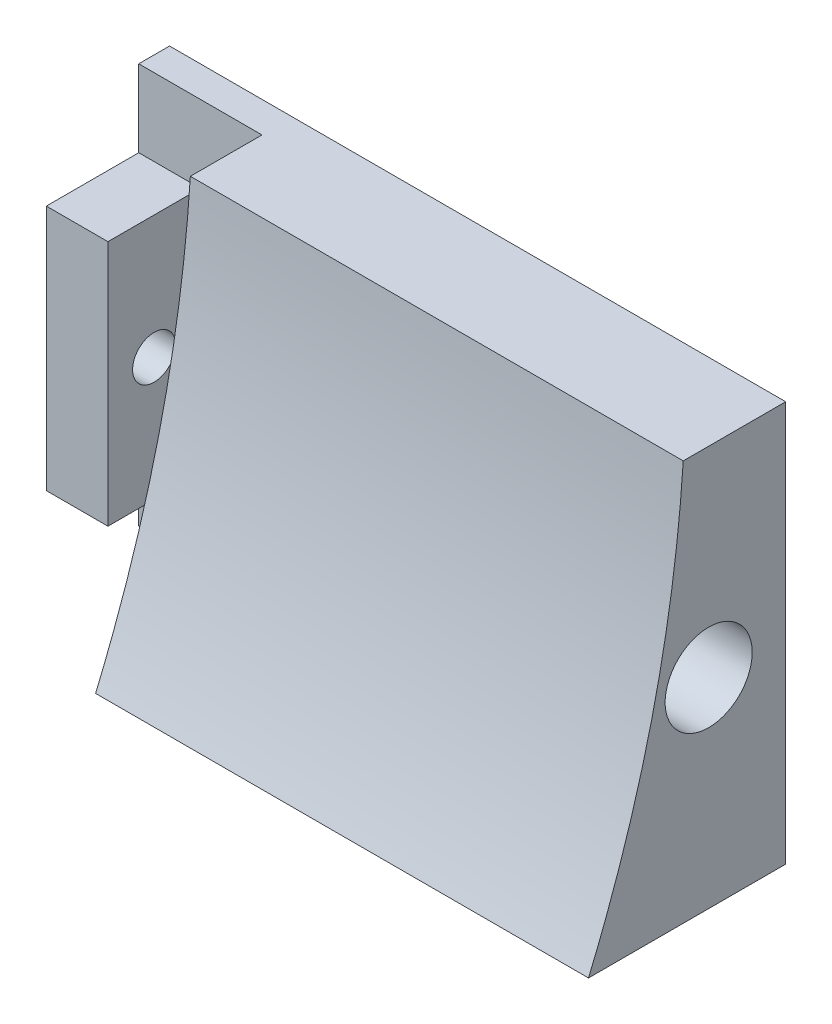
SolidWorks part; units mm, degrees
ref_plane "Plan de face" through (0, 0, 0) normal (0, 0, 1) x (1, 0, 0)
ref_plane "Plan de dessus" through (0, 0, 0) normal (0, 1, 0) x (1, 0, 0)
ref_plane "Plan de droite" through (0, 0, 0) normal (1, 0, 0) x (0, 0, -1)
sketch "Esquisse1" plane through (0, 0, 0) normal (0, 0, 1) x (1, 0, 0)
  line L0 (28, -11.85) -> (28, -37.85)
  line L1 (0, 0) -> (0, -49.7) construction
  line L2 (28, -24.85) -> (-3.4703, -24.85) construction
  line L3 (0, -24.85) -> (-8.0205, -24.85) construction
  line L4 (-12, -11.85) -> (-12, -37.85) construction
  line L5 (28, -11.85) -> (-12, -11.85)
  line L6 (-12, -11.85) -> (-12, -37.85)
  line L7 (-12, -37.85) -> (28, -37.85)
  dimension "D1" = 49.7
  dimension "D2" = 28
  dimension "D3" = 26
  dimension "D4" = 0
  dimension "D5" = 12
extrude "Boss.-Extru.1" add sketch "Esquisse1" along normal blind 2
sketch "Esquisse2" plane through (-12, 0, 0) normal (-1, 0, 0) x (0, 0, 1)
  line L0 (2, -24.85) -> (0, -24.85) construction
  line L1 (2, -11.85) -> (2, -37.85) construction
  line L2 (0, -11.85) -> (0, -37.85) construction
  line L3 (0, -32.85) -> (8, -32.85) construction
  line L4 (8, -32.85) -> (8, -24.85) construction
  line L5 (8, -24.85) -> (2, -24.85) construction
  line L6 (4, -32.85) -> (4, -24.85) construction
  line L7 (2, -32.85) -> (2, -24.85) construction
  line L8 (0, -16.85) -> (0, -32.85)
  line L9 (0, -32.85) -> (8, -32.85)
  line L10 (8, -32.85) -> (8, -16.85)
  line L11 (0, -16.85) -> (8, -16.85)
  dimension "D1" = 8
  dimension "D2" = 2
  dimension "D3" = 8
extrude "Boss.-Extru.2" add sketch "Esquisse2" against normal blind 4
sketch "Esquisse3" plane through (-12, 0, 0) normal (-1, 0, 0) x (0, 0, 1)
  line L0 (5, -32.85) -> (5, -16.85) construction
  line L1 (2, -32.85) -> (8, -32.85) construction
  line L2 (8, -16.85) -> (2, -16.85) construction
  line L3 (8, -24.85) -> (0, -24.85) construction
  line L4 (8, -32.85) -> (8, -16.85) construction
  line L5 (0, -11.85) -> (0, -37.85) construction
  circle A0 centre (5, -24.85) radius 1.4
extrude "Enlèv. mat.-Extru.1" cut sketch "Esquisse3" against normal blind 4
sketch "Esquisse4" plane through (28, 0, 0) normal (1, 0, 0) x (0, 0, -1)
  line L0 (0, -11.85) -> (-6.65, -11.85) construction
  line L1 (0, -37.85) -> (-12.8, -37.85) construction
  line L2 (-6.65, -11.85) -> (0, -11.85)
  line L3 (0, -11.85) -> (0, -37.85)
  line L4 (0, -37.85) -> (-12.8, -37.85)
  spline S0 degree 2 poles (-6.65, -11.85) (-7.5506, -25.3842) (-12.8, -37.85) knots 0 0 0 1 1 1
extrude "Boss.-Extru.3" add sketch "Esquisse4" against normal blind 32
sketch "Esquisse5" plane through (-12, 0, 0) normal (-1, 0, 0) x (0, 0, 1)
  circle A0 centre (5, -24.85) radius 1.4
extrude "Enlèv. mat.-Extru.2" cut sketch "Esquisse5" against normal blind 41
sketch "Esquisse6" plane through (28, 0, 0) normal (1, 0, 0) x (0, 0, -1)
  circle A0 centre (-5, -24.85) radius 2.8266
extrude "Enlèv. mat.-Extru.3" cut sketch "Esquisse6" against normal blind 32
